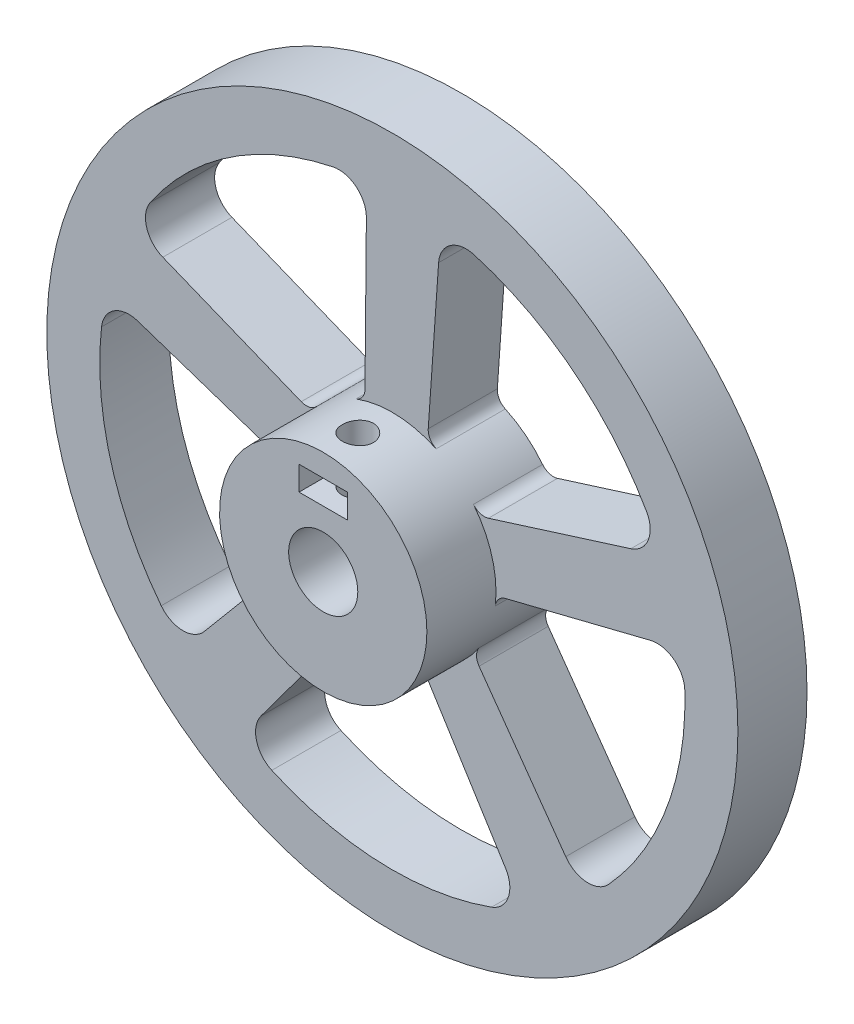
SolidWorks part; units mm, degrees
ref_plane "Plan de face" through (0, 0, 0) normal (0, 0, 1) x (1, 0, 0)
ref_plane "Plan de dessus" through (0, 0, 0) normal (0, 1, 0) x (1, 0, 0)
ref_plane "Plan de droite" through (0, 0, 0) normal (1, 0, 0) x (0, 0, -1)
sketch "Esquisse1" plane through (0, 0, 0) normal (0, 0, 1) x (1, 0, 0)
  circle A0 centre (0, 0) radius 5
  circle A1 centre (0, 0) radius 15
  dimension "D1" = 10
  dimension "D2" = 30
extrude "Boss.-Extru.4" add sketch "Esquisse1" along normal blind 10
sketch "Esquisse3" plane through (0, 0, 0) normal (0, 0, 1) x (1, 0, 0)
  circle A0 centre (0, 0) radius 50
extrude "Boss.-Extru.5" add sketch "Esquisse3" against normal blind 10
sketch "Esquisse14" plane through (0, 0, 0) normal (0, 0, 1) x (1, 0, 0)
  circle A0 centre (0, 0) radius 5
extrude "Enlèv. mat.-Extru.1" cut sketch "Esquisse14" against normal blind 10
sketch "Esquisse19" plane through (0, 0, 0) normal (0, 0, 1) x (1, 0, 0)
  line L1 (-13.3386, -9.5219) -> (-27.219, -26.0777)
  line L5 (-36.8329, 8.0159) -> (-16.3481, 1.1507)
  line L6 (-13.1777, 9.7433) -> (-33.2125, 17.8283)
  line L12 (-3.7584, 37.5072) -> (-3.9575, 15.9036)
  line L13 (5.1943, 15.5436) -> (6.6925, 37.0962)
  line L15 (-19.0056, -32.5531) -> (-6.1462, -15.1924)
  line L16 (4.934, -15.6282) -> (16.3902, -33.9452)
  line L17 (34.5101, 15.1648) -> (13.9023, 8.6783)
  line L18 (16.388, -0.1368) -> (37.3487, 5.0984)
  line L19 (25.0868, -28.1348) -> (12.5495, -10.5401)
  circle A2 centre (0, 0) radius 15 construction
  arc A8 (-4.0051, -14.4554) -> (2.8574, -14.7253) centre (0, 0) ccw
  arc A19 (-17.4389, -38.5789) -> (14.3551, -39.8293) centre (0, 0) ccw
  arc A25 (-4.0051, -14.4554) -> (-6.1462, -15.1924) centre (-4.5391, -16.3828) ccw
  arc A28 (-17.4389, -38.5789) -> (-19.0056, -32.5531) centre (-15.7913, -34.934) cw
  arc A29 (14.3551, -39.8293) -> (16.3902, -33.9452) centre (12.9989, -36.0663) ccw
  arc A30 (4.934, -15.6282) -> (2.8574, -14.7253) centre (3.2384, -16.6887) ccw
  arc A31 (-33.444, -25.9605) -> (-27.219, -26.0777) centre (-30.2842, -23.5078) ccw
  arc A32 (-42.0796, 4.6639) -> (-33.444, -25.9605) centre (0, 0) ccw
  arc A33 (-42.0796, 4.6639) -> (-36.8329, 8.0159) centre (-38.104, 4.2232) cw
  arc A34 (-14.9856, -0.6579) -> (-13.1216, -7.2679) centre (0, 0) ccw
  arc A35 (-14.9856, -0.6579) -> (-16.3481, 1.1507) centre (-16.9836, -0.7457) ccw
  arc A36 (-13.3386, -9.5219) -> (-13.1216, -7.2679) centre (-14.8712, -8.237) ccw
  arc A37 (-35.0247, 23.7849) -> (-33.2125, 17.8283) centre (-31.7155, 21.5377) ccw
  arc A38 (-8.5677, 41.4613) -> (-35.0247, 23.7849) centre (0, 0) ccw
  arc A39 (-8.5677, 41.4613) -> (-3.7584, 37.5072) centre (-7.7582, 37.5441) cw
  arc A40 (-5.2565, 14.0488) -> (-10.967, 10.2335) centre (0, 0) ccw
  arc A41 (-5.2565, 14.0488) -> (-3.9575, 15.9036) centre (-5.9574, 15.922) ccw
  arc A42 (-13.1777, 9.7433) -> (-10.967, 10.2335) centre (-12.4293, 11.598) ccw
  arc A43 (11.7975, 40.6604) -> (6.6925, 37.0962) centre (10.6829, 36.8188) ccw
  arc A44 (36.7845, 20.9606) -> (11.7975, 40.6604) centre (0, 0) ccw
  arc A45 (36.7845, 20.9606) -> (34.5101, 15.1648) centre (33.3091, 18.9803) cw
  arc A46 (11.7369, 9.3406) -> (6.3436, 13.5926) centre (0, 0) ccw
  arc A47 (11.7369, 9.3406) -> (13.9023, 8.6783) centre (13.3018, 10.586) ccw
  arc A48 (5.1943, 15.5436) -> (6.3436, 13.5926) centre (7.1895, 15.4049) ccw
  arc A49 (42.3159, 1.3446) -> (37.3487, 5.0984) centre (38.318, 1.2176) ccw
  arc A50 (31.3018, -28.5069) -> (42.3159, 1.3446) centre (0, 0) ccw
  arc A51 (31.3018, -28.5069) -> (25.0868, -28.1348) centre (28.3444, -25.8136) cw
  arc A52 (12.5103, -8.276) -> (14.8876, -1.8328) centre (0, 0) ccw
  arc A53 (12.5103, -8.276) -> (12.5495, -10.5401) centre (14.1783, -9.3795) ccw
  arc A54 (16.388, -0.1368) -> (14.8876, -1.8328) centre (16.8726, -2.0772) ccw
  point P67 (4.1711, -14.4084)
  point P68 (0, 0)
  point P70 (9.9304, -11.2422)
  dimension "D5" = 5
  dimension "D4" = 42.3373
  dimension "D3" = 21.6046
  dimension "D17" = 2
  dimension "D18" = 4
  dimension "D19" = 4
  dimension "D20" = 2
extrude "Enlèv. mat.-Extru.7" cut sketch "Esquisse19" against normal blind 10
sketch "Esquisse20" plane through (0, 0, 0) normal (0, 1, 0) x (1, 0, 0)
  circle A1 centre (0, -5) radius 2.25
  dimension "D1" = 4.5
extrude "Enlèv. mat.-Extru.8" cut sketch "Esquisse20" along normal up to next
sketch "Esquisse25" plane through (0, 0, 0) normal (0, 0, 1) x (1, 0, 0)
  line L0 (-3.5, 11.75) -> (3.5, 11.75)
  line L2 (3.5, 11.75) -> (3.5, 8.25)
  line L3 (-3.5, 8.25) -> (-3.5, 11.75)
  line L4 (-3.5, 8.25) -> (3.5, 8.25)
  dimension "D1" = 7
  dimension "D2" = 3.5
  dimension "D3" = 8.25
  dimension "D4" = 3.5
extrude "Enlèv. mat.-Extru.10" cut sketch "Esquisse25" along normal blind 10
sketch "Esquisse16" plane through (0, 0, 0) normal (0, 0, 1) x (1, 0, 0)
  line L0 (0, 15) -> (0, 40)
  line L1 (38.0423, 12.3607) -> (14.2658, 4.6353)
  circle A0 centre (0, 0) radius 10 construction
  arc A1 (0, 40) -> (38.0423, 12.3607) centre (0, 0) cw
  arc A2 (0, 15) -> (14.2658, 4.6353) centre (0, 0) cw
  dimension "D1" = 25
